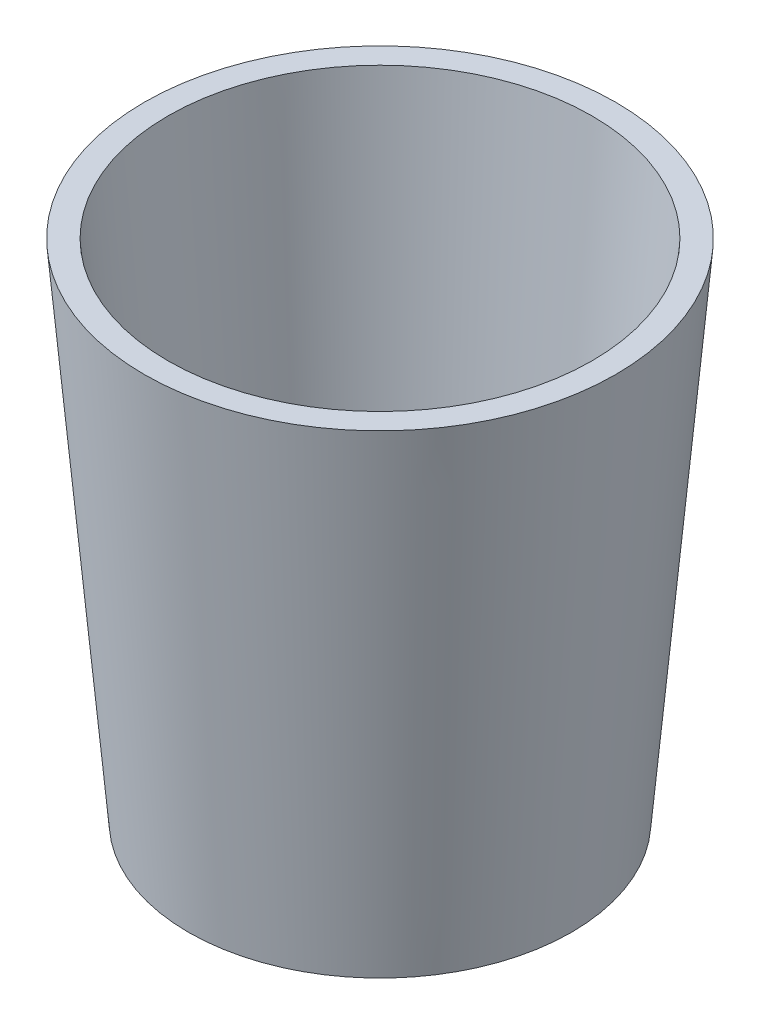
SolidWorks part; units mm, degrees
ref_plane "前视基准面" through (0, 0, 0) normal (0, 0, 1) x (1, 0, 0)
ref_plane "上视基准面" through (0, 0, 0) normal (0, 1, 0) x (1, 0, 0)
ref_plane "右视基准面" through (0, 0, 0) normal (1, 0, 0) x (0, 0, -1)
other "Configuration Table"
sketch "草图2" plane through (0, 0, 0) normal (1, 0, 0) x (0, 0, -1)
  line L0 (-13.1233, 150) -> (0, 0)
  line L1 (0, 0) -> (56.8767, 0)
  line L2 (56.8767, 0) -> (56.8767, 20)
  line L3 (56.8767, 20) -> (5.277, 20)
  line L4 (5.277, 20) -> (-6.0966, 150)
  line L5 (-6.0966, 150) -> (-13.1233, 150)
  point P5 (0, 0)
  dimension "D1" = 85
  dimension "D2" = 150
  dimension "D3" = 20
  dimension "D4" = 7
  dimension "D5" = 70
revolve "旋转1" add sketch "草图2" angle 360 about L2
